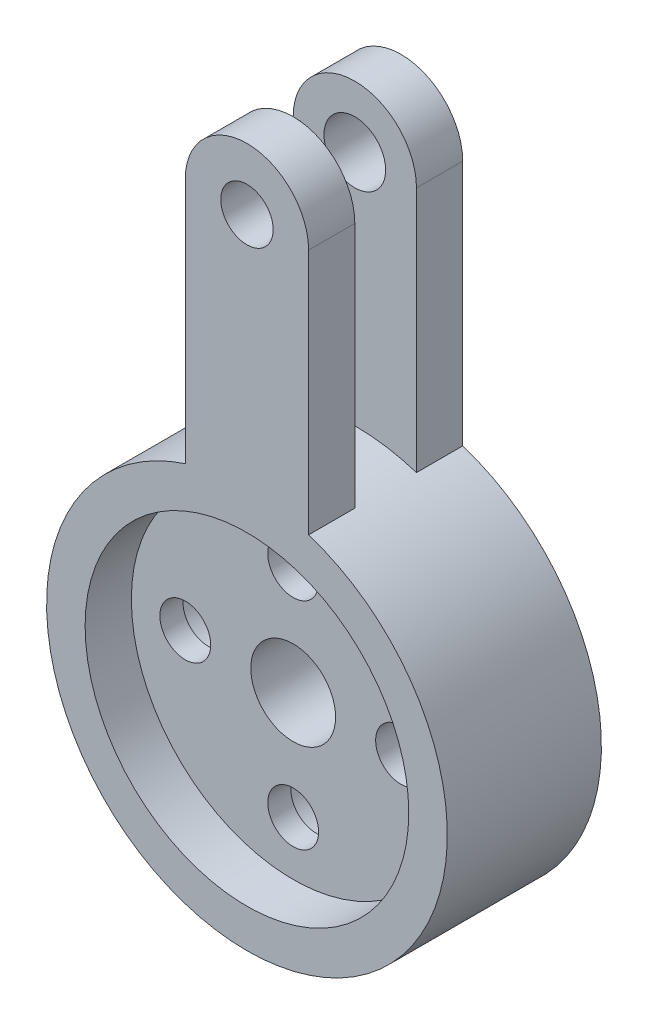
SolidWorks part; units mm, degrees
ref_plane "Plan de face" through (0, 0, 0) normal (0, 0, 1) x (1, 0, 0)
ref_plane "Plan de dessus" through (0, 0, 0) normal (0, 1, 0) x (1, 0, 0)
ref_plane "Plan de droite" through (0, 0, 0) normal (1, 0, 0) x (0, 0, -1)
sketch "Esquisse1" plane through (0, 0, 0) normal (0, 0, 1) x (1, 0, 0)
  line L0 (-7, 0) -> (0, 0) construction
  circle A0 centre (0, 0) radius 13
  circle A1 centre (0, 0) radius 2.75
  circle A2 centre (-7, 0) radius 1.65
  circle A3 centre (0, 7) radius 1.65
  circle A4 centre (7, 0) radius 1.65
  circle A5 centre (0, -7) radius 1.65
  point P15 (0, 0)
  dimension "D1" = 26
  dimension "D2" = 5.5
  dimension "D3" = 3.3
  dimension "D4" = 7
  dimension "D5" = 4
extrude "Boss.-Extru.1" add sketch "Esquisse1" along normal blind 10
sketch "Esquisse2" plane through (0, 0, 10) normal (0, 0, 1) x (1, 0, 0)
  circle A0 centre (0, 0) radius 10.5
  dimension "D1" = 21
extrude "Enlèv. mat.-Extru.1" cut sketch "Esquisse2" against normal blind 3
sketch "Esquisse3" plane through (0, 0, 0) normal (0, 0, -1) x (-1, 0, 0)
  circle A0 centre (-7, 0) radius 2.75
  circle A1 centre (0, 7) radius 2.75
  circle A2 centre (7, 0) radius 2.75
  circle A3 centre (0, -7) radius 2.75
  dimension "D1" = 5.5
extrude "Enlèv. mat.-Extru.2" cut sketch "Esquisse3" against normal blind 5.5
sketch "Esquisse4" plane through (0, 0, 0) normal (0, 0, -1) x (-1, 0, 0)
  line L0 (-4, 28.3693) -> (4, 28.3693) construction
  line L1 (-4, 12.3693) -> (4, 12.3693) construction
  line L2 (-4, 12.3693) -> (-4, 32.3693) construction
  line L3 (-4, 32.3693) -> (4, 32.3693) construction
  line L4 (4, 12.3693) -> (4, 32.3693) construction
  line L5 (-4, 28.3693) -> (-4, 12.3693)
  line L6 (4, 28.3693) -> (4, 12.3693)
  arc A0 (-4, 12.3693) -> (4, 12.3693) centre (0, 0) cw
  circle A1 centre (0, 0) radius 13 construction
  arc A2 (-4, 28.3693) -> (4, 28.3693) centre (0, 28.3693) cw
  circle A3 centre (0, 28.3693) radius 1.7
  dimension "D3" = 3.4
  dimension "D1" = 8
  dimension "D2" = 20
extrude "Boss.-Extru.2" add sketch "Esquisse4" against normal blind 3
ref_plane "Plan1" through (0, 0, 5) normal (0, 0, 1) x (1, 0, 0)
mirror "Symétrie1" about plane through (0, 0, 5) normal (0, 0, 1) of "Boss.-Extru.2"
sketch "Esquisse5" plane through (0, 0, 0) normal (0, 0, -1) x (-1, 0, 0)
  circle A0 centre (0, 28.3693) radius 2
  dimension "D1" = 4
extrude "Enlèv. mat.-Extru.3" cut sketch "Esquisse5" against normal blind 3
